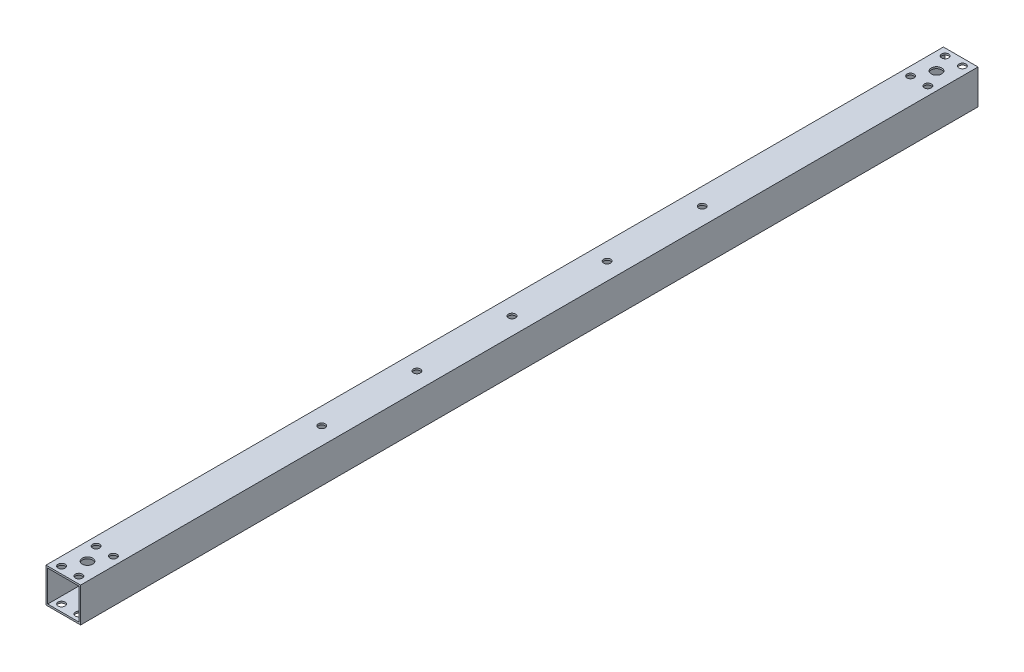
SolidWorks part; units mm, degrees
material "1060 合金"
ref_plane "前视基准面" through (0, 0, 0) normal (0, 0, 1) x (1, 0, 0)
ref_plane "上视基准面" through (0, 0, 0) normal (0, 1, 0) x (1, 0, 0)
ref_plane "右视基准面" through (0, 0, 0) normal (1, 0, 0) x (0, 0, -1)
other "Configuration Table"
sketch "草图1" plane through (0, 0, 0) normal (0, 0, 1) x (1, 0, 0)
  line L0 (-10, -10) -> (-10, 10)
  line L1 (-9, -9) -> (9, -9)
  line L2 (-9, -9) -> (-9, 9)
  line L3 (-9, 9) -> (9, 9)
  line L4 (9, -9) -> (9, 9)
  line L5 (-9, -9) -> (9, 9) construction
  line L6 (-9, 9) -> (9, -9) construction
  line L7 (-10, 10) -> (10, 10)
  line L8 (10, -10) -> (10, 10)
  line L9 (-10, -10) -> (10, -10)
  point P0 (0, 0)
  dimension "D2" = 20
  dimension "D1" = 1
extrude "凸台-拉伸1" add sketch "草图1" along normal mid plane 519
sketch "草图2" plane through (0, 10, 0) normal (0, 1, 0) x (1, 0, 0)
  line L0 (0, 0) -> (0, 50000) construction
  line L1 (10, 259.5) -> (-10, 259.5) construction
  line L2 (-5, 235.5) -> (5, 235.5) construction
  line L3 (-5, 235.5) -> (-5, 255.5) construction
  line L4 (-5, 255.5) -> (5, 255.5) construction
  line L5 (5, 235.5) -> (5, 255.5) construction
  line L6 (-5, 235.5) -> (5, 255.5) construction
  line L7 (-5, 255.5) -> (5, 235.5) construction
  line L8 (0, 0) -> (50000, 0) construction
  circle A0 centre (-5, 255.5) radius 2.025
  circle A1 centre (5, 255.5) radius 2.025
  circle A2 centre (-5, 235.5) radius 2.025
  circle A3 centre (5, 235.5) radius 2.025
  circle A4 centre (0, 245.5) radius 3.025
  circle A5 centre (5, -235.5) radius 2.025
  circle A6 centre (-5, -235.5) radius 2.025
  circle A7 centre (-5, -255.5) radius 2.025
  circle A8 centre (0, -245.5) radius 3.025
  circle A9 centre (5, -255.5) radius 2.025
  point P3 (0, 245.5)
  dimension "D4" = 4.05
  dimension "D5" = 6.05
  dimension "D1" = 4
  dimension "D2" = 20
  dimension "D3" = 10
extrude "切除-拉伸1" cut sketch "草图2" against normal mid plane 40
sketch "草图3" plane through (0, 10, 0) normal (0, 1, 0) x (1, 0, 0)
  line L0 (0, 110) -> (0, -110) construction
  circle A0 centre (0, 110) radius 2.025
  circle A1 centre (0, 55) radius 2.025
  circle A2 centre (0, 0) radius 2.025
  circle A3 centre (0, -55) radius 2.025
  circle A4 centre (0, -110) radius 2.025
  point P4 (0, 0)
  dimension "D2" = 4.05
  dimension "D1" = 220
  dimension "D3" = 5
extrude "切除-拉伸2" cut sketch "草图3" against normal blind 20
